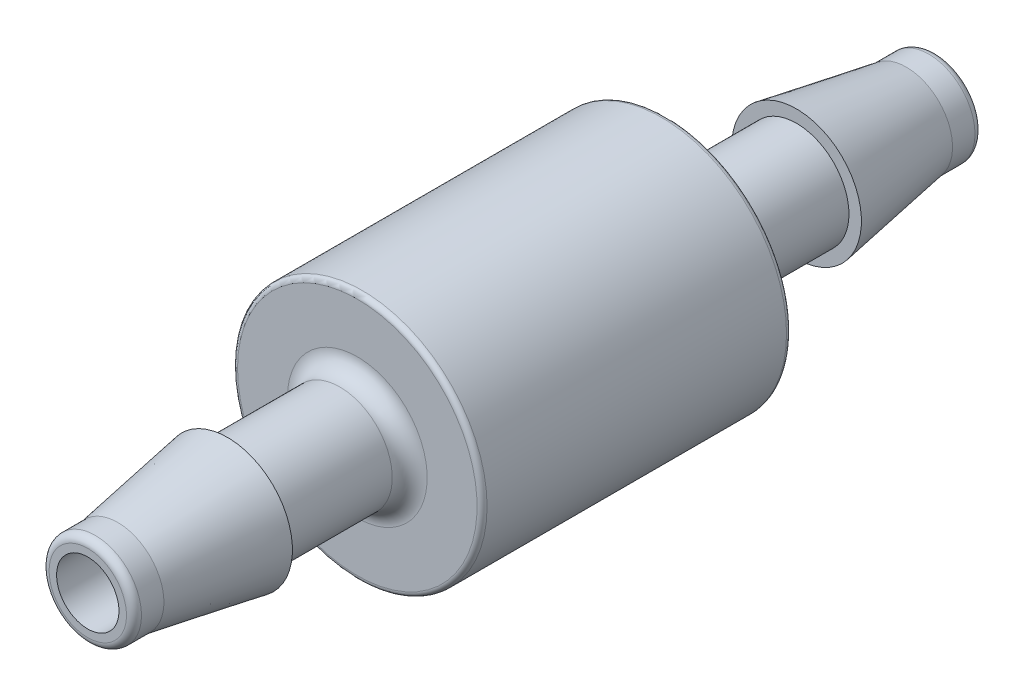
SolidWorks part; units mm, degrees
ref_plane "Front Plane" through (0, 0, 0) normal (0, 0, 1) x (1, 0, 0)
ref_plane "Top Plane" through (0, 0, 0) normal (0, 1, 0) x (1, 0, 0)
ref_plane "Right Plane" through (0, 0, 0) normal (1, 0, 0) x (0, 0, -1)
sketch "Sketch1" plane through (0, 0, 0) normal (1, 0, 0) x (0, 0, -1)
  line L0 (-21.59, 0) -> (21.59, 0) construction
  line L1 (21.59, 6.35) -> (21.59, -6.35) construction
  line L2 (-21.59, 1.5875) -> (-21.59, -1.5875) construction
  line L4 (-21.59, 2.3813) -> (-21.59, -2.3813) construction
  line L8 (-21.59, 6.35) -> (-21.59, -6.35) construction
  point P20 (-7.874, 0)
  point P21 (7.874, 0)
  dimension "OD" = 12.7
  dimension "Lg." = 43.18
  dimension "ID" = 3.175
  dimension "L1" = 13.716
  dimension "L2" = 15.748
  dimension "L3" = 13.716
  dimension "Tube ID" = 4.7625
sketch "Sketch2" plane through (0, 0, 0) normal (1, 0, 0) x (0, 0, -1)
  line L0 (21.59, 0) -> (-21.59, 0) construction
  line L1 (21.59, 6.35) -> (21.59, -6.35) construction
  line L2 (-21.59, 1.5875) -> (-21.59, -1.5875) construction
  line L3 (-21.59, 1.5875) -> (-21.59, 1.9685)
  line L4 (14.478, 2.667) -> (8.763, 2.667)
  line L5 (21.209, 2.3495) -> (20.066, 2.3495)
  line L6 (7.874, 3.556) -> (7.874, 6.096)
  line L7 (21.59, 1.5875) -> (21.59, 1.9685)
  line L8 (-7.874, 3.556) -> (-7.874, 6.096)
  line L9 (-7.62, 6.35) -> (7.62, 6.35)
  line L10 (14.478, 3.302) -> (14.478, 2.667)
  line L11 (20.066, 2.3495) -> (14.478, 3.302)
  line L14 (0, 0) -> (0, 6.35) construction
  line L15 (-21.209, 2.3495) -> (-20.066, 2.3495)
  line L17 (-20.066, 2.3495) -> (-14.478, 3.302)
  line L18 (-14.478, 3.302) -> (-14.478, 2.667)
  line L19 (-14.478, 2.667) -> (-8.763, 2.667)
  line L24 (-21.59, 1.5875) -> (21.59, 1.5875)
  arc A0 (7.874, 6.096) -> (7.62, 6.35) centre (7.62, 6.096) ccw
  arc A1 (-7.874, 6.096) -> (-7.62, 6.35) centre (-7.62, 6.096) cw
  arc A2 (-21.209, 2.3495) -> (-21.59, 1.9685) centre (-21.209, 1.9685) ccw
  arc A3 (21.209, 2.3495) -> (21.59, 1.9685) centre (21.209, 1.9685) cw
  arc A4 (-8.763, 2.667) -> (-7.874, 3.556) centre (-8.763, 3.556) ccw
  arc A5 (8.763, 2.667) -> (7.874, 3.556) centre (8.763, 3.556) cw
  dimension "D3" = 6.604
  dimension "D4" = 5.588
  dimension "D5" = 5.334
  dimension "R1" = 0.254
  dimension "R2" = 0.381
  dimension "R3" = 0.889
  dimension "D1" = 4.699
  dimension "D2" = 1.524
revolve "Revolve1" add sketch "Sketch2" angle 360 mid plane about L0
sketch "SketchX" plane through (0, 0, 0) normal (1, 0, 0) x (0, 0, -1)
  line L10 (21.59, 1.5875) -> (-21.59, 1.5875) construction
  line L12 (-21.59, -1.5875) -> (21.59, -1.5875) construction
  line L13 (21.59, 1.5875) -> (-21.59, 1.5875)
  line L14 (-21.59, -1.5875) -> (21.59, -1.5875)
